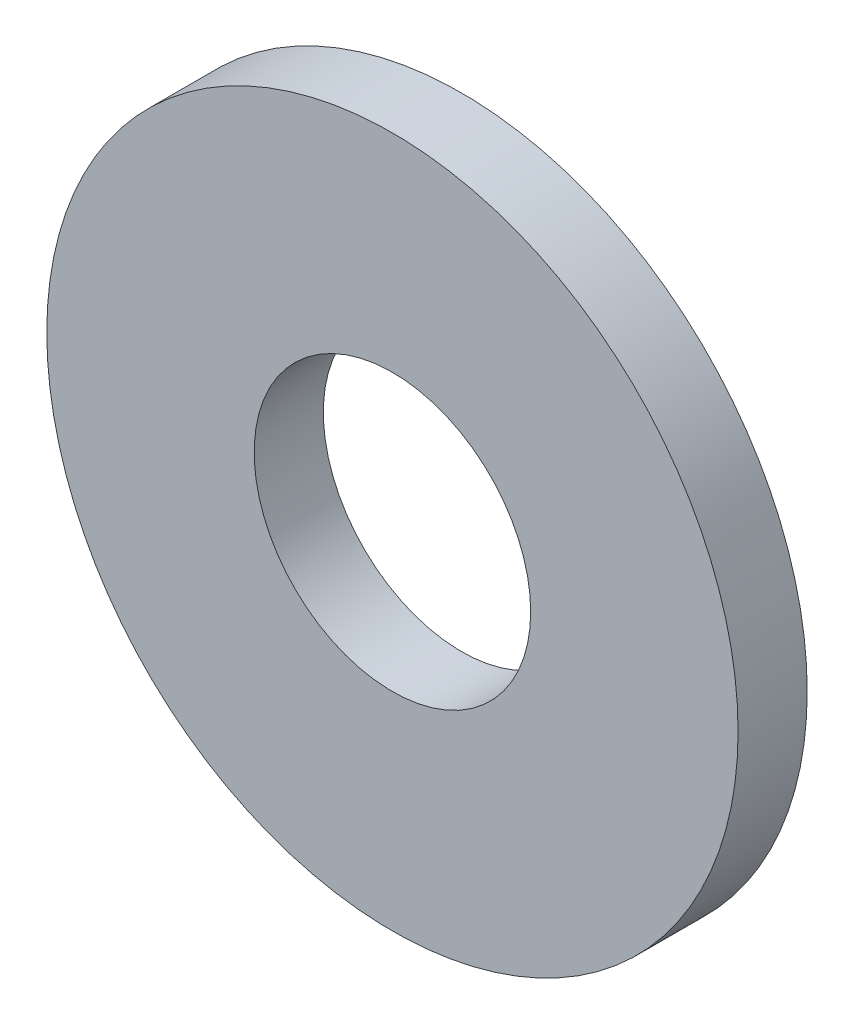
SolidWorks part; units mm, degrees
material "Brass"
ref_plane "Front Plane" through (0, 0, 0) normal (0, 0, 1) x (1, 0, 0)
ref_plane "Top Plane" through (0, 0, 0) normal (0, 1, 0) x (1, 0, 0)
ref_plane "Right Plane" through (0, 0, 0) normal (1, 0, 0) x (0, 0, -1)
sketch "Sketch1" plane through (0, 0, 0) normal (0, 0, 1) x (1, 0, 0)
  circle A1 centre (0, 0) radius 15.875
  dimension "D2" = 31.75
extrude "Boss-Extrude1" add sketch "Sketch1" along normal blind 3.175 contours A1
sketch "Sketch2" plane through (0, 0, 0) normal (0, 0, 1) x (1, 0, 0)
  circle A0 centre (0, 0) radius 6.35
  dimension "D1" = 12.7
extrude "Cut-Extrude1" cut sketch "Sketch2" along normal up to surface (3.175 mm away) up to face at (15.875, 0, 3.175)
